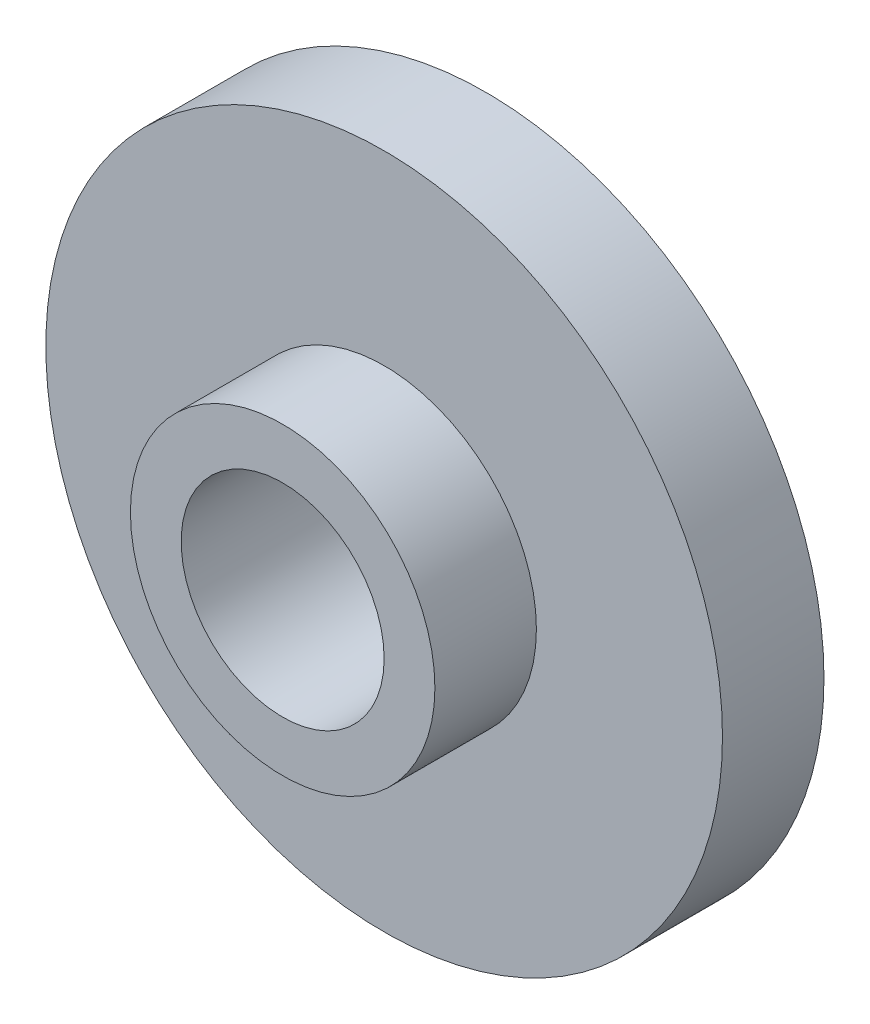
SolidWorks part; units mm, degrees
ref_plane "Front Plane" through (0, 0, 0) normal (0, 0, 1) x (1, 0, 0)
ref_plane "Top Plane" through (0, 0, 0) normal (0, 1, 0) x (1, 0, 0)
ref_plane "Right Plane" through (0, 0, 0) normal (1, 0, 0) x (0, 0, -1)
sketch "Sketch1" plane through (0, 0, 0) normal (0, 0, 1) x (1, 0, 0)
  line L0 (-5.2478, 0) -> (5.8929, 0) construction
  line L1 (0, 4.7945) -> (0, -7.0036) construction
  circle A0 centre (0, 0) radius 3
  circle A1 centre (0, 0) radius 10
  dimension "D1" = 6
extrude "Boss-Extrude1" add sketch "Sketch1" along normal blind 3
ref_plane "Plane1" through (0, 0, 3) normal (0, 0, 1) x (1, 0, 0)
sketch "Sketch2" plane through (0, 0, 3) normal (0, 0, 1) x (1, 0, 0)
  circle A0 centre (0, 0) radius 3
  circle A2 centre (0, 0) radius 4.5
  dimension "D1" = 6
extrude "Boss-Extrude2" add sketch "Sketch2" along normal blind 3
